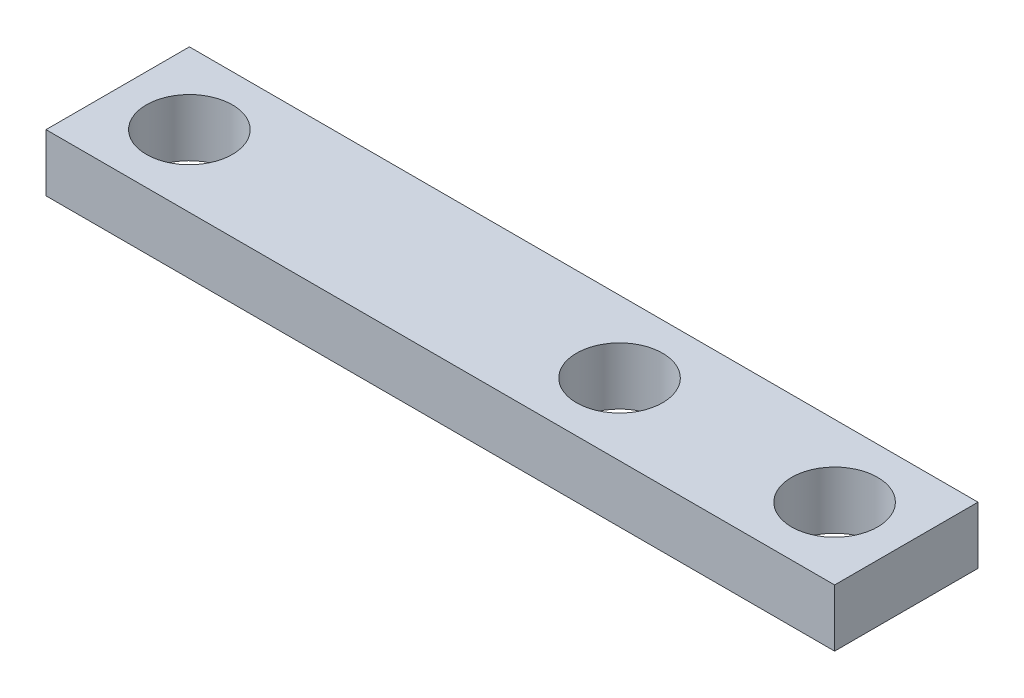
SolidWorks part; units mm, degrees
ref_plane "Front Plane" through (0, 0, 0) normal (0, 0, 1) x (1, 0, 0)
ref_plane "Top Plane" through (0, 0, 0) normal (0, 1, 0) x (1, 0, 0)
ref_plane "Right Plane" through (0, 0, 0) normal (1, 0, 0) x (0, 0, -1)
sketch "Sketch1" plane through (0, 0, 0) normal (0, 1, 0) x (1, 0, 0)
  line L4 (9.525, 0) -> (9.525, 3.175) construction
  line L5 (12.7, -3.175) -> (-22.225, -3.175)
  line L6 (12.7, -3.175) -> (12.7, 3.175)
  line L7 (12.7, 3.175) -> (-22.225, 3.175)
  line L8 (-22.225, -3.175) -> (-22.225, 3.175)
  line L9 (9.525, 0) -> (12.7, 0) construction
  line L10 (-19.05, 0) -> (-19.05, 3.175) construction
  line L11 (-19.05, 0) -> (-22.225, 0) construction
  circle A0 centre (-19.05, 0) radius 1.905
  circle A1 centre (9.525, 0) radius 1.905
  circle A2 centre (0, 0) radius 1.905
  point P9 (-22.225, 0)
  dimension "D2" = 3.81
  dimension "D5" = 3.81
  dimension "D1" = 9.525
  dimension "D3" = 19.05
  dimension "D4" = 6.35
extrude "Boss-Extrude1" add sketch "Sketch1" along normal blind 2.54
